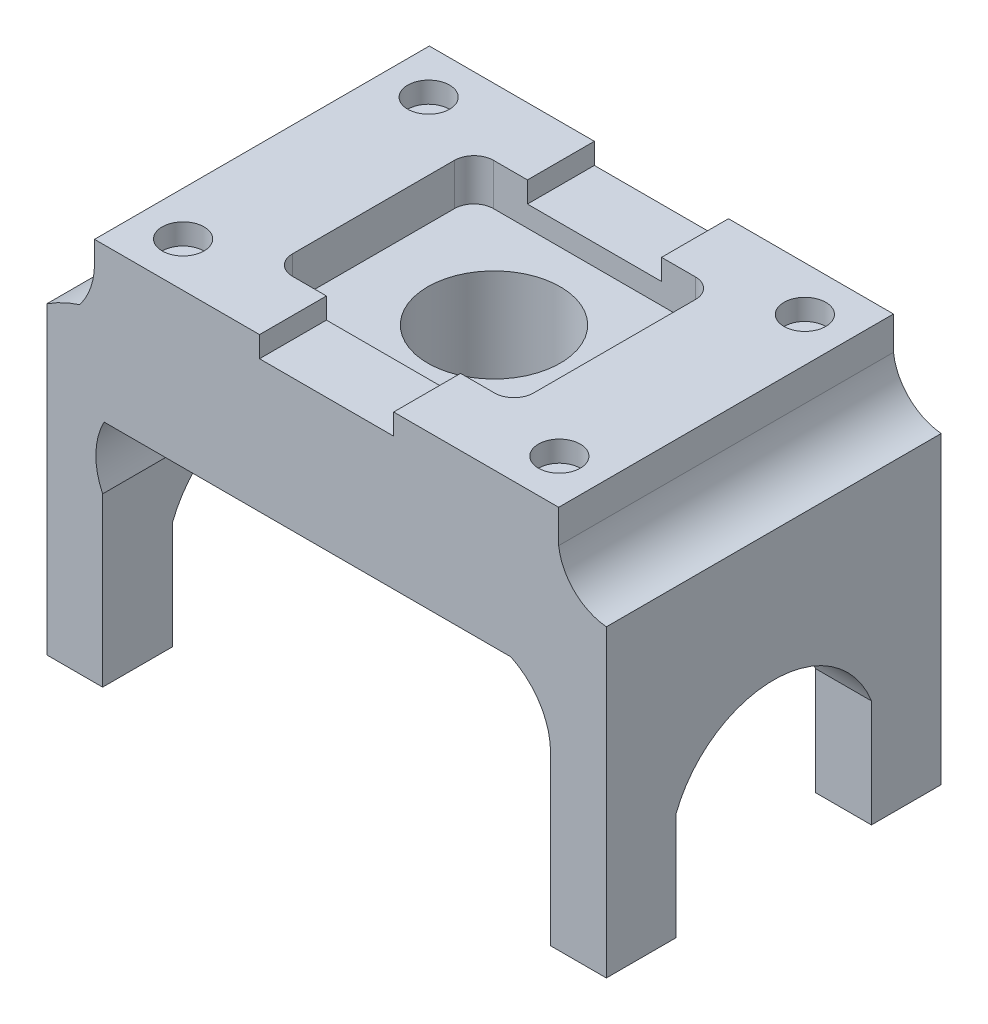
SolidWorks part; units mm, degrees
ref_plane "Front Plane" through (0, 0, 0) normal (0, 0, 1) x (1, 0, 0)
ref_plane "Top Plane" through (0, 0, 0) normal (0, 1, 0) x (1, 0, 0)
ref_plane "Right Plane" through (0, 0, 0) normal (1, 0, 0) x (0, 0, -1)
sketch "Sketch1" plane through (0, 0, 0) normal (0, 0, 1) x (1, 0, 0)
  line L0 (40.7761, -15.7843) -> (40.7761, 14.6957)
  line L1 (40.7761, -15.7843) -> (-40.5039, -15.7843) construction
  line L2 (33.5521, 26.1545) -> (-40.5039, 26.1545)
  line L3 (-40.7761, -15.7843) -> (-50.9361, -15.7843)
  line L4 (-40.7761, -15.7843) -> (-40.7761, 14.6957)
  line L5 (40.7761, -15.7843) -> (50.9361, -15.7843)
  line L6 (-50.9361, -15.7843) -> (-50.9361, 39.5877)
  line L7 (-29.3098, 26.1545) -> (-29.3098, 50.2845) construction
  line L8 (-29.3098, 50.2845) -> (-42.2519, 50.2845)
  line L10 (0, 55.245) -> (0, -20.7534) construction
  line L11 (29.3098, 50.2845) -> (42.2519, 50.2845)
  line L12 (50.9361, -15.7843) -> (50.9361, 39.5877)
  line L13 (42.2519, 48.0428) -> (42.2519, 50.2845)
  line L14 (-29.3098, 50.2845) -> (29.3098, 50.2845)
  arc A0 (40.7761, 14.6957) -> (33.5521, 26.1545) centre (28.0761, 14.6957) ccw
  arc A1 (-40.7761, 14.6957) -> (-40.5039, 26.1545) centre (-29.3098, 20.156) cw
  arc A3 (50.9361, 39.5877) -> (42.2519, 48.0428) centre (51.8346, 49.1978) cw
  arc A4 (-42.2519, 50.2845) -> (-44.9601, 42.4453) centre (-54.9519, 50.2845) cw
  arc A5 (-50.9361, 39.5877) -> (-44.9601, 42.4453) centre (-37.0843, 18.2971) cw
  dimension "D2" = 12.7
  dimension "D6" = 24.13
  dimension "D7" = 12.7
  dimension "D8" = 25.4
  dimension "D1" = 30.48
  dimension "D3" = 81.28
  dimension "D4" = 10.16
  dimension "D5" = 55.372
extrude "Boss-Extrude1" add sketch "Sketch1" along normal blind 60.96
sketch "Sketch4" plane through (0, 46.4745, 0) normal (0, 1, 0) x (1, 0, 0)
  line L0 (0, -7.8868) -> (0, -53.0732) construction
  line L1 (16.542, -7.8868) -> (-16.542, -7.8868) construction
  line L2 (-16.542, -53.0732) -> (16.542, -53.0732) construction
  circle A0 centre (0, -30.48) radius 12.065
  dimension "D1" = 24.13
extrude "Cut-Extrude3" cut sketch "Sketch4" against normal blind 3.81
sketch "Sketch6" plane through (50.9361, 0, 0) normal (1, 0, 0) x (0, 0, -1)
  line L0 (-60.96, -15.7843) -> (-48.26, -15.7843)
  line L1 (-60.96, -15.7843) -> (0, -15.7843) construction
  line L2 (-48.26, -15.7843) -> (-48.26, 3.7737)
  line L3 (-30.48, -15.7843) -> (-30.48, 9.1468) construction
  line L4 (0, -15.7843) -> (-12.7, -15.7843)
  line L5 (-12.7, -15.7843) -> (-12.7, 3.7737)
  arc A0 (-48.26, 3.7737) -> (-12.7, 3.7737) centre (-30.48, -3.0654) cw
  dimension "D3" = 19.05
  dimension "D1" = 12.7
  dimension "D2" = 19.558
extrude "Cut-Extrude4" cut sketch "Sketch6" against normal through all and the other way through all
sketch "Sketch7" plane through (0, 50.2845, 0) normal (0, 1, 0) x (1, 0, 0)
  line L0 (-42.2519, -30.48) -> (-26.2499, -30.48) construction
  line L2 (-42.2519, -60.96) -> (-42.2519, 0) construction
  line L3 (-42.2519, -60.96) -> (-16.1723, -60.96) construction
  line L4 (42.2519, -60.96) -> (-42.2519, -60.96) construction
  line L5 (-34.2509, -60.96) -> (-34.2509, -52.832) construction
  line L6 (0, 0) -> (0, -60.96) construction
  line L7 (-12.2087, 0) -> (11.9213, 0)
  line L8 (42.2519, 0) -> (-42.2519, 0) construction
  line L9 (-12.2087, 0) -> (-42.2519, 0)
  line L10 (-42.2519, 0) -> (-42.2519, -60.96)
  line L11 (-42.2519, -60.96) -> (-12.2087, -60.96)
  line L12 (-12.2087, -60.96) -> (-12.2087, -48.7778)
  line L13 (-12.2087, -48.7778) -> (-18.3903, -48.7778)
  line L14 (-12.2087, 0) -> (-12.2087, -12.1822)
  line L15 (-12.2087, -12.1822) -> (-18.3903, -12.1822)
  line L16 (-21.9463, -15.7382) -> (-21.9463, -45.2218)
  line L17 (42.2519, -60.96) -> (12.2087, -60.96)
  line L18 (42.2519, 0) -> (42.2519, -60.96)
  line L19 (12.2087, 0) -> (42.2519, 0)
  line L20 (12.2087, 0) -> (12.2087, -12.1822)
  line L21 (12.2087, -60.96) -> (12.2087, -48.7778)
  line L22 (12.2087, -48.7778) -> (18.3903, -48.7778)
  line L23 (21.9463, -15.7382) -> (21.9463, -45.2218)
  line L24 (12.2087, -12.1822) -> (18.3903, -12.1822)
  circle A0 centre (-34.2509, -52.832) radius 3.81
  circle A1 centre (34.2509, -52.832) radius 3.81
  circle A2 centre (-34.2509, -8.128) radius 3.81
  circle A3 centre (34.2509, -8.128) radius 3.81
  arc A4 (-18.3903, -12.1822) -> (-21.9463, -15.7382) centre (-18.3903, -15.7382) ccw
  arc A5 (-18.3903, -48.7778) -> (-21.9463, -45.2218) centre (-18.3903, -45.2218) cw
  arc A6 (18.3903, -48.7778) -> (21.9463, -45.2218) centre (18.3903, -45.2218) ccw
  arc A7 (18.3903, -12.1822) -> (21.9463, -15.7382) centre (18.3903, -15.7382) cw
  point P5 (0, 0)
  point P27 (-0.1437, 0)
  line M16 (42.2519, 0) -> (-42.2519, 0)
  line M17 (-42.2519, 0) -> (-42.2519, -60.96)
  line M18 (-42.2519, -60.96) -> (42.2519, -60.96)
  line M19 (42.2519, -60.96) -> (42.2519, 0)
  dimension "D3" = 7.62
  dimension "D5" = 3.556
  dimension "D6" = 3.556
  dimension "D1" = 16.002
  dimension "D2" = 8.128
  dimension "D4" = 24.13
extrude "Boss-Extrude3" add sketch "Sketch7" along normal blind 3.81 contours L13 A5 L16 A4 L15 L14 L12 A2 A0 M16 M17 M18 | L24 A7 L23 A6 L22 L21 L20 A3 A1 M18 M19 M16
sketch "Sketch8" plane through (0, 50.2845, 0) normal (0, 1, 0) x (1, 0, 0)
  line L0 (-21.9463, -15.7382) -> (-21.9463, -45.2218)
  line L1 (-18.3903, -12.1822) -> (18.3903, -12.1822)
  line L2 (-18.3903, -12.1822) -> (-18.3903, -48.7778)
  line L3 (-18.3903, -48.7778) -> (18.3903, -48.7778)
  line L4 (18.3903, -12.1822) -> (18.3903, -48.7778)
  line L5 (-18.3903, -12.1822) -> (-18.3903, -48.7778)
  line L6 (18.3903, -12.1822) -> (18.3903, -48.7778)
  line L7 (21.9463, -15.7382) -> (21.9463, -45.2218)
  arc A0 (-18.3903, -12.1822) -> (-21.9463, -15.7382) centre (-18.3903, -15.7382) ccw
  arc A1 (-18.3903, -48.7778) -> (-21.9463, -45.2218) centre (-18.3903, -45.2218) cw
  arc A2 (18.3903, -12.1822) -> (21.9463, -15.7382) centre (18.3903, -15.7382) cw
  arc A3 (21.9463, -15.7382) -> (18.3903, -12.1822) centre (18.3903, -15.7382) ccw construction
  arc A4 (21.9463, -45.2218) -> (18.3903, -48.7778) centre (18.3903, -45.2218) cw
  line M7 (12.2087, -48.7778) -> (18.3903, -48.7778)
  arc M8 (18.3903, -48.7778) -> (21.9463, -45.2218) centre (18.3903, -45.2218) ccw
  line M9 (21.9463, -45.2218) -> (21.9463, -15.7382)
  arc M10 (21.9463, -15.7382) -> (18.3903, -12.1822) centre (18.3903, -15.7382) ccw
  line M11 (18.3903, -12.1822) -> (12.2087, -12.1822)
  line M15 (-12.2087, -12.1822) -> (-18.3903, -12.1822)
  arc M16 (-18.3903, -12.1822) -> (-21.9463, -15.7382) centre (-18.3903, -15.7382) ccw
  line M17 (-21.9463, -15.7382) -> (-21.9463, -45.2218)
  arc M18 (-21.9463, -45.2218) -> (-18.3903, -48.7778) centre (-18.3903, -45.2218) ccw
  line M19 (-18.3903, -48.7778) -> (-12.2087, -48.7778)
extrude "Cut-Extrude7" cut sketch "Sketch8" against normal blind 3.81 contours L4 L1 L2 L3 M11 M15 M19 M7 | L2 M16 M17 M18 | L4 M10 M8 M9
sketch "Sketch11" plane through (0, 0, 0) normal (0, 1, 0) x (1, 0, 0)
  circle A0 centre (0, -30.48) radius 12.065
extrude "Cut-Extrude8" cut sketch "Sketch11" along normal blind 114.3
